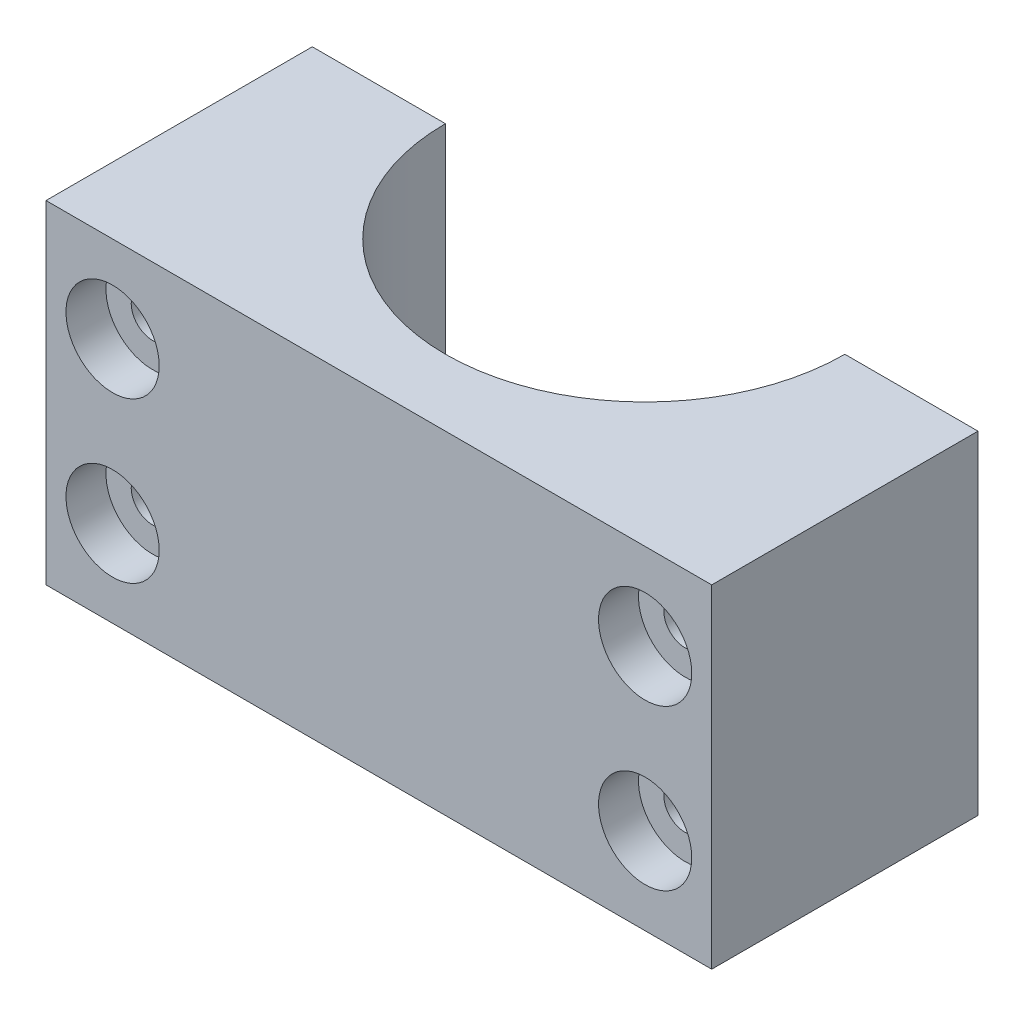
SolidWorks part; units mm, degrees
ref_plane "Спереди" through (0, 0, 0) normal (0, 0, 1) x (1, 0, 0)
ref_plane "Сверху" through (0, 0, 0) normal (0, 1, 0) x (1, 0, 0)
ref_plane "Справа" through (0, 0, 0) normal (1, 0, 0) x (0, 0, -1)
sketch "Sketch1" plane through (0, 0, 0) normal (0, 1, 0) x (1, 0, 0)
  line L0 (25.0276, 0) -> (-24.9724, 0) construction
  line L1 (-14.9724, 0) -> (-24.9724, 0)
  line L2 (-24.9724, 0) -> (-24.9724, -20)
  line L3 (-24.9724, -20) -> (-4.9724, -20)
  line L4 (-4.9724, -20) -> (-4.9724, -45)
  line L5 (-4.9724, -45) -> (5.0276, -45)
  line L6 (5.0276, -45) -> (5.0276, -20)
  line L7 (5.0276, -20) -> (25.0276, -20)
  line L8 (25.0276, -20) -> (25.0276, 0)
  line L9 (15.0276, 0) -> (25.0276, 0)
  circle A0 centre (0.0276, 0) radius 15 construction
  arc A1 (-14.9724, 0) -> (15.0276, 0) centre (0.0276, 0) ccw
  dimension "D2" = 30
  dimension "D1" = 50
  dimension "D3" = 10
  dimension "D4" = 25
  dimension "D5" = 20
extrude "Boss-Extrude1" add sketch "Sketch1" along normal blind 25
sketch "Sketch2" plane through (-4.9724, 0, 0) normal (-1, 0, 0) x (0, 0, 1)
  line L0 (45, 12.5) -> (20, 12.5) construction
  line L1 (45, 25) -> (45, 0) construction
  line L2 (20, 25) -> (20, 0) construction
  circle A0 centre (36, 12.5) radius 4
  dimension "D1" = 8
  dimension "D2" = 9
extrude "Cut-Extrude1" cut sketch "Sketch2" against normal through all
sketch "Sketch3" plane through (0, 0, 0) normal (0, 0, -1) x (-1, 0, 0)
  line L0 (-20.0276, 0) -> (-20.0276, 25) construction
  line L1 (-25.0276, 0) -> (-15.0276, 0) construction
  line L2 (-25.0276, 25) -> (-15.0276, 25) construction
  line L3 (19.9724, 0) -> (19.9724, 25) construction
  line L4 (14.9724, 0) -> (24.9724, 0) construction
  line L5 (14.9724, 25) -> (24.9724, 25) construction
  line L6 (-20.0276, 6.5) -> (19.9724, 6.5) construction
  line L7 (-20.0276, 18.5) -> (19.9724, 18.5) construction
  circle A0 centre (-20.0276, 6.5) radius 1.6
  circle A1 centre (-20.0276, 18.5) radius 1.6
  circle A2 centre (19.9724, 6.5) radius 1.6
  circle A3 centre (19.9724, 18.5) radius 1.6
  point P16 (-20.0276, 12.5)
  dimension "D2" = 3.2
  dimension "D3" = 12
  dimension "D4" = 6
extrude "Cut-Extrude2" cut sketch "Sketch3" against normal through all
sketch "Sketch4" plane through (0, 25, 0) normal (0, 1, 0) x (1, 0, 0)
  line L0 (-4.9724, -20) -> (5.0276, -20)
  line L1 (5.0276, -20) -> (5.0276, -45)
  line L2 (5.0276, -45) -> (-4.9724, -45)
  line L3 (-4.9724, -45) -> (-4.9724, -20)
extrude "Cut-Extrude3" cut sketch "Sketch4" against normal through all
sketch "Sketch5" plane through (0, 0, 20) normal (0, 0, 1) x (1, 0, 0)
  circle A0 centre (20.0276, 18.5) radius 3.5
  circle A1 centre (20.0276, 6.5) radius 3.5
  circle A2 centre (-19.9724, 6.5) radius 3.5
  circle A3 centre (-19.9724, 18.5) radius 3.5
  dimension "D1" = 7
extrude "Cut-Extrude4" cut sketch "Sketch5" against normal blind 3
